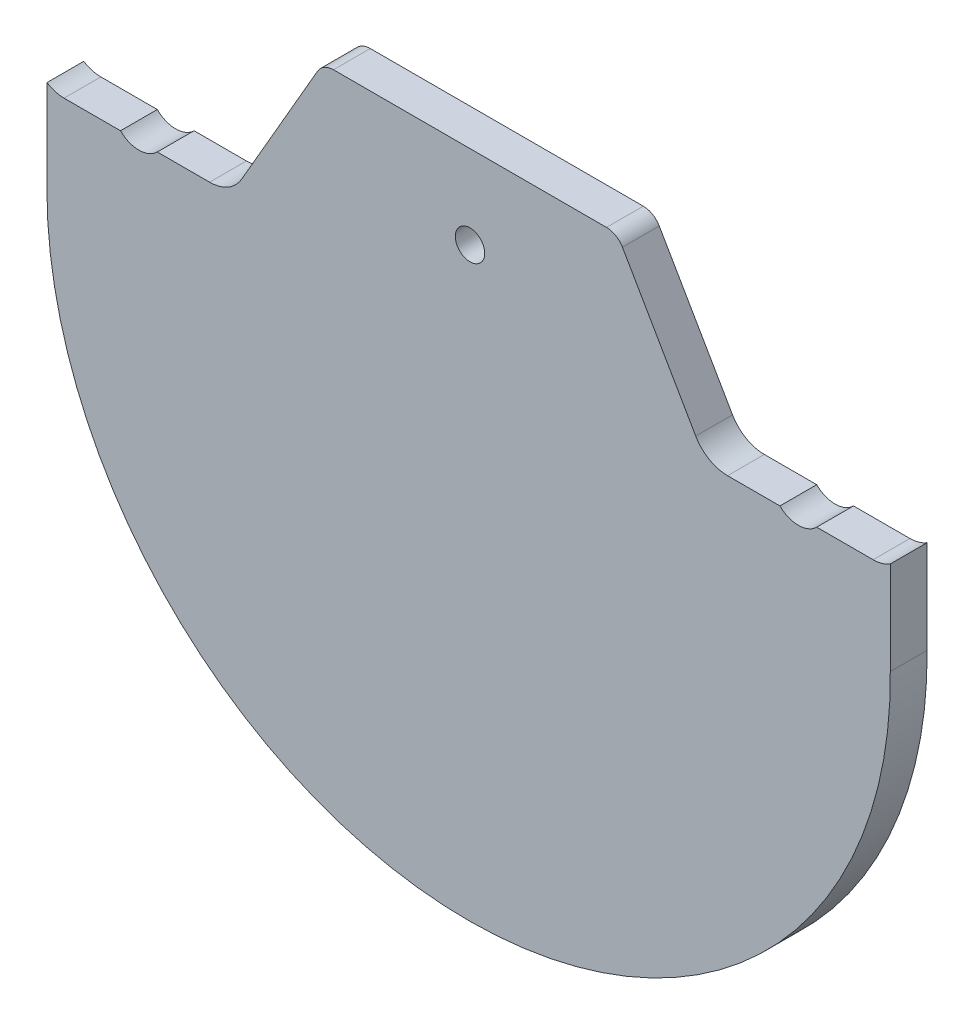
SolidWorks part; units mm, degrees
material "Balsa"
ref_plane "Ebene vorne" through (0, 0, 0) normal (0, 0, 1) x (1, 0, 0)
ref_plane "Ebene oben" through (0, 0, 0) normal (0, 1, 0) x (1, 0, 0)
ref_plane "Ebene rechts" through (0, 0, 0) normal (1, 0, 0) x (0, 0, -1)
sketch "Skizze2" plane through (0, 0, 0) normal (0, 0, 1) x (1, 0, 0)
  line L0 (1.4434, 0) -> (38.5566, 0)
  line L1 (40.7217, -1.25) -> (50.6801, -18.4986)
  line L2 (40, 14.0859) -> (40, -17.6492) construction
  line L3 (55.0103, -20.9986) -> (62.1235, -20.9986)
  line L4 (67.1235, -20.9986) -> (74.7933, -20.9986)
  line L5 (77.1235, -20.3287) -> (77.1235, -32.9986)
  line L6 (-27.5, -21.6506) -> (-35.17, -21.6506)
  line L7 (-37.501, -20.9806) -> (-37.5, -33.6506)
  line L8 (0, 11.7679) -> (0, -17.6492) construction
  line L9 (-0.7217, -1.25) -> (-11.0566, -19.1506)
  line L10 (-15.3868, -21.6506) -> (-22.5, -21.6506)
  line L17 (19.8136, 38.5591) -> (19.8136, -113.1503) construction
  arc A0 (40.7217, -1.25) -> (38.5566, 0) centre (38.5566, -2.5) ccw
  arc A1 (55.0103, -20.9986) -> (50.6801, -18.4986) centre (55.0103, -15.9986) cw
  arc A2 (-0.7217, -1.25) -> (1.4434, 0) centre (1.4434, -2.5) cw
  arc A3 (-15.3868, -21.6506) -> (-11.0566, -19.1506) centre (-15.3868, -16.6506) ccw
  arc A4 (-37.5, -33.6506) -> (77.1235, -32.9986) centre (19.8136, -33.6506) ccw
  arc A5 (-35.17, -21.6506) -> (-37.501, -20.9806) centre (-35.17, -17.2606) cw
  arc A6 (74.7933, -20.9986) -> (77.1235, -20.3287) centre (74.7933, -16.6107) ccw
  arc A8 (67.1235, -20.9986) -> (62.1235, -20.9986) centre (64.6235, -18.4986) cw
  arc A9 (-27.5, -21.6506) -> (-22.5, -21.6506) centre (-25, -19.1506) ccw
  point P8 (40, 0)
  point P16 (52.1235, -20.9986)
  point P22 (0, 0)
  point P30 (-12.5, -21.6506)
  point P34 (-25, -22.6862)
  dimension "D2" = 2.5
  dimension "D4" = 30
  dimension "D9" = 5
  dimension "D12" = 2.5
  dimension "D17" = 5
  dimension "D20" = 57.3136
  dimension "D21" = 12.67
  dimension "D22" = 4.3879
  dimension "D6" = 3.5355
  dimension "D14" = 3.5355
  dimension "D16" = 4.39
  dimension "D25" = 2.5
  dimension "D1" = 40
  dimension "D3" = 25
  dimension "D5" = 10
  dimension "D7" = 2.5
  dimension "D8" = 7.6698
  dimension "D10" = 25
  dimension "D11" = 30
  dimension "D13" = 10
  dimension "D15" = 7.67
  dimension "D18" = 12.6699
  dimension "D19" = 12
  dimension "D24" = 12
  dimension "D26" = 12.5
extrude "Aufsatz-Linear austragen1" add sketch "Skizze2" along normal blind 5
hole_wizard "Ø4.0 (4) Durchmesser Bohrung1" positions "Skizze3" profile "Skizze4" hole size "Ø4.0" standard "DIN"
sketch "Skizze3" plane through (0, 0, 5) normal (0, 0, 1) x (1, 0, 0)
  point P0 (20, -11.3301)
sketch "Skizze4" plane through (20, -11.3301, 5) normal (1, 0, 0) x (0, -1, 0)
  line L0 (0, 0) -> (0, 6.2017)
  line L1 (0, 6.2017) -> (2, 5)
  line L2 (2, 5) -> (2, 0)
  line L5 (2, 0) -> (0, 0)
  line L10 (0, 6.2017) -> (-2, 5) construction
  line L11 (0, -6.35) -> (0, 107.95) construction
  dimension "Bohrerdurchmesser" = 4
  dimension "Bohrungstiefe" = 5
  dimension "Spitzenwinkel" = 118
